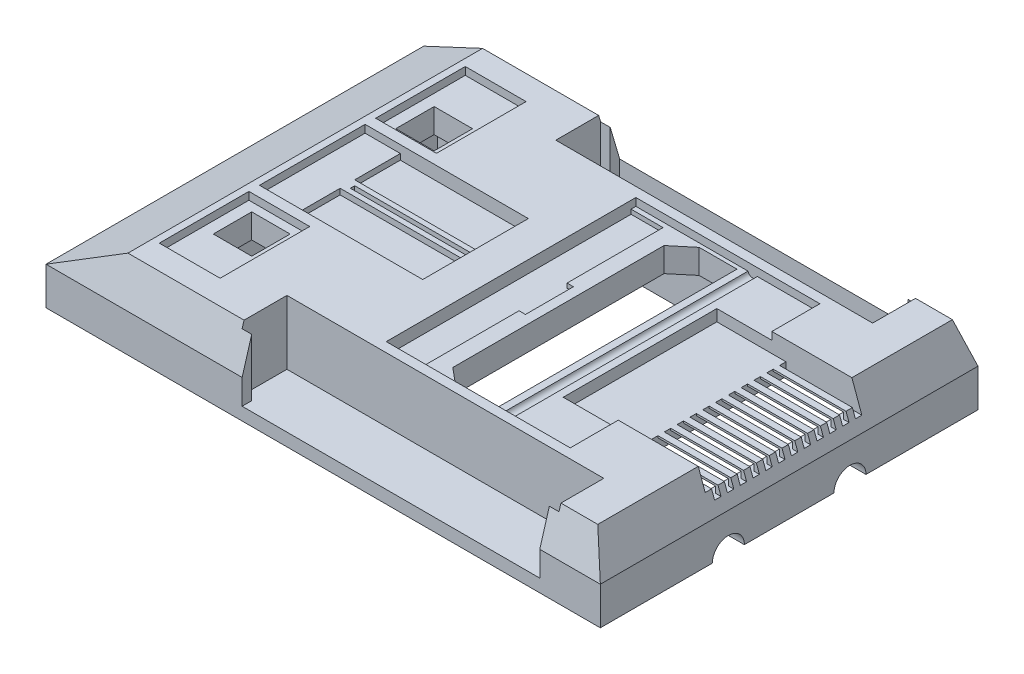
SolidWorks part; units mm, degrees
ref_plane "Front Plane" through (0, 0, 0) normal (0, 0, 1) x (1, 0, 0)
ref_plane "Top Plane" through (0, 0, 0) normal (0, 1, 0) x (1, 0, 0)
ref_plane "Right Plane" through (0, 0, 0) normal (1, 0, 0) x (0, 0, -1)
sketch "Sketch1" plane through (0, 0, 0) normal (0, 1, 0) x (1, 0, 0)
  line L1 (-219.964, -149.86) -> (0, -149.86)
  line L2 (-219.964, -149.86) -> (-219.964, 0)
  line L3 (-219.964, 0) -> (0, 0)
  line L4 (0, -149.86) -> (0, 0)
  dimension "D1" = 149.86
  dimension "D2" = 219.964
ref_plane "MiddleTop" through (0, 14.986, 0) normal (0, 1, 0) x (1, 0, 0)
sketch "Sketch2" plane through (0, 14.986, 0) normal (0, 1, 0) x (1, 0, 0)
  line L1 (0, 0) -> (-219.964, 0)
  line L2 (0, 0) -> (0, -149.86)
  line L3 (0, -149.86) -> (-219.964, -149.86)
  line L4 (-219.964, 0) -> (-219.964, -149.86)
extrude "Boss-Extrude1" add sketch "Sketch1" along normal blind 14.986
ref_plane "Plane2" through (0, 30.48, 0) normal (0, 1, 0) x (1, 0, 0)
sketch "Sketch3" plane through (0, 30.48, 0) normal (0, 1, 0) x (1, 0, 0)
  line L0 (0, -149.86) -> (-219.964, -149.86) construction
  line L1 (-192.024, -4.572) -> (-5.588, -4.572)
  line L2 (-192.024, -4.572) -> (-192.024, -145.288)
  line L3 (-192.024, -145.288) -> (-5.588, -145.288)
  line L4 (-5.588, -4.572) -> (-5.588, -145.288)
  line L5 (-219.964, 0) -> (-219.964, -149.86) construction
  line L6 (0, 0) -> (0, -149.86) construction
  dimension "D1" = 140.716
  dimension "D2" = 4.572
  dimension "D3" = 27.94
  dimension "D4" = 5.588
loft "Loft1" add profiles "Sketch2", "Sketch3"
sketch "Sketch4" plane through (0, 30.48, 0) normal (0, 1, 0) x (1, 0, 0)
  line L0 (-192.024, -145.288) -> (-5.588, -145.288) construction
  line L1 (-189.23, -135.636) -> (-165.1, -135.636)
  line L2 (-189.23, -135.636) -> (-189.23, -100.076)
  line L3 (-189.23, -100.076) -> (-165.1, -100.076)
  line L4 (-165.1, -135.636) -> (-165.1, -100.076)
  line L5 (-192.024, -4.572) -> (-192.024, -145.288) construction
  line L6 (-5.588, -4.572) -> (-192.024, -4.572) construction
  line L7 (-189.23, -49.784) -> (-165.1, -49.784)
  line L8 (-189.23, -49.784) -> (-189.23, -14.224)
  line L9 (-189.23, -14.224) -> (-165.1, -14.224)
  line L10 (-165.1, -49.784) -> (-165.1, -14.224)
  point P12 (-177.165, -14.224)
  dimension "D1" = 35.56
  dimension "D2" = 24.13
  dimension "D3" = 9.652
  dimension "D4" = 2.794
  dimension "D5" = 24.13
  dimension "D6" = 35.56
  dimension "D7" = 2.794
  dimension "D8" = 9.652
sketch "Sketch5" plane through (0, 30.48, 0) normal (0, 1, 0) x (1, 0, 0)
  line L0 (-189.23, -100.076) -> (-165.1, -100.076) construction
  line L1 (-189.23, -95.885) -> (-124.46, -95.885)
  line L2 (-189.23, -95.885) -> (-189.23, -53.975)
  line L3 (-189.23, -53.975) -> (-124.46, -53.975)
  line L4 (-124.46, -95.885) -> (-124.46, -53.975)
  line L5 (-192.024, -4.572) -> (-192.024, -145.288) construction
  dimension "D1" = 41.91
  dimension "D2" = 4.191
  dimension "D3" = 2.794
  dimension "D4" = 64.77
extrude "Cut-Extrude1" cut sketch "Sketch4" against normal blind 3.048
extrude "Cut-Extrude2" cut sketch "Sketch5" against normal blind 3.048
ref_plane "Plane3" through (0, 25.146, 0) normal (0, 1, 0) x (1, 0, 0)
sketch "Sketch6" plane through (0, 25.146, 0) normal (0, 1, 0) x (1, 0, 0)
  line L0 (-189.23, -53.975) -> (-189.23, -95.885) construction
  line L1 (-175.26, -72.0598) -> (-124.46, -72.0598)
  line L2 (-175.26, -72.0598) -> (-175.26, -77.851)
  line L3 (-175.26, -77.851) -> (-124.46, -77.851)
  line L4 (-124.46, -72.0598) -> (-124.46, -77.851)
  line L5 (-189.23, -95.885) -> (-124.46, -95.885) construction
  dimension "D1" = 50.8
  dimension "D2" = 13.97
  dimension "D3" = 5.7912
  dimension "D4" = 18.034
sketch "Sketch10" plane through (0, 30.48, 0) normal (0, 1, 0) x (1, 0, 0)
  line L6 (0, -16.7641) -> (0, 16.7641) construction
  line L10 (-145.9491, -146.0512) -> (-145.9491, -128.2712)
  line L13 (-145.9491, -128.2712) -> (-20.2191, -128.2712)
  line L16 (-20.2191, -128.2712) -> (-20.2191, -146.0512)
  line L21 (-20.2191, -146.0512) -> (-145.9491, -146.0512)
  line L24 (-16.7641, 0) -> (16.7641, 0) construction
  line L25 (-219.964, -74.93) -> (-5.588, -74.93) construction
  line L26 (-20.2191, -21.5888) -> (-20.2191, -3.8088)
  line L27 (-219.964, 0) -> (-219.964, -149.86) construction
  line L28 (-5.588, -145.288) -> (-5.588, -4.572) construction
  line L29 (-20.2191, -3.8088) -> (-145.9491, -3.8088)
  line L30 (-145.9491, -3.8088) -> (-145.9491, -21.5888)
  line L31 (-145.9491, -21.5888) -> (-20.2191, -21.5888)
  dimension "D1" = 17.78
  dimension "D2" = 20.2191
  dimension "D3" = 128.2712
  dimension "D5" = 125.73
extrude "Cut-Extrude5" cut sketch "Sketch10" against normal blind 25.4
sketch "Sketch15" plane through (0, 30.48, 0) normal (0, 1, 0) x (1, 0, 0)
  line L0 (-5.588, -145.288) -> (-5.588, -4.572) construction
  line L1 (-110.363, -25.4) -> (-37.338, -25.4)
  line L2 (-110.363, -25.4) -> (-110.363, -124.46)
  line L3 (-110.363, -124.46) -> (-37.338, -124.46)
  line L4 (-37.338, -25.4) -> (-37.338, -44.45)
  line L6 (-37.338, -44.45) -> (-59.182, -44.45)
  line L7 (-59.182, -44.45) -> (-59.182, -105.41)
  line L8 (-59.182, -105.41) -> (-37.338, -105.41)
  line L9 (-37.338, -105.41) -> (-37.338, -124.46)
  line L10 (0, 0) -> (-219.964, 0) construction
  dimension "D1" = 73.025
  dimension "D2" = 31.75
  dimension "D3" = 99.06
  dimension "D4" = 25.4
  dimension "D5" = 21.844
  dimension "D6" = 60.96
  dimension "D7" = 19.05
extrude "Cut-Extrude7" cut sketch "Sketch15" against normal blind 3.048
sketch "Sketch16" plane through (0, 30.48, 0) normal (0, 1, 0) x (1, 0, 0)
  line L1 (-59.182, -44.45) -> (0.508, -44.45)
  line L2 (-59.182, -44.45) -> (-59.182, -105.41)
  line L3 (-59.182, -105.41) -> (0.508, -105.41)
  line L4 (0.508, -44.45) -> (0.508, -105.41)
  dimension "D1" = 59.69
extrude "Cut-Extrude8" cut sketch "Sketch16" against normal blind 7.62
sketch "Sketch17" plane through (0, 30.48, 0) normal (0, 1, 0) x (1, 0, 0)
  line L1 (-110.363, -27.3038) -> (-97.663, -27.3038)
  line L2 (-110.363, -27.3038) -> (-110.363, -122.5538)
  line L3 (-110.363, -122.5538) -> (-97.663, -122.5538)
  line L4 (-97.663, -27.3038) -> (-97.663, -65.4038)
  line L5 (-97.663, -65.4038) -> (-95.123, -65.4038)
  line L6 (-95.123, -65.4038) -> (-95.123, -84.4538)
  line L7 (-95.123, -84.4538) -> (-97.663, -84.4538)
  line L8 (-97.663, -84.4538) -> (-97.663, -122.5538)
  line L9 (-37.338, -21.5888) -> (-110.363, -21.5888) construction
  line L11 (-124.46, -95.885) -> (-124.46, -53.975) construction
  dimension "D1" = 12.7
  dimension "D2" = 19.05
  dimension "D3" = 38.1
  dimension "D4" = 2.54
  dimension "D5" = 95.25
  dimension "D6" = 5.715
  dimension "D7" = 14.097
extrude "Cut-Extrude9" cut sketch "Sketch17" against normal blind 4.826
sketch "Sketch18" plane through (0, 30.48, 0) normal (0, 1, 0) x (1, 0, 0)
  line L0 (-83.71, -26.9228) -> (-91.313, -33.2728)
  line L1 (-83.71, -26.9228) -> (-68.724, -26.9228)
  line L2 (-91.313, -33.2728) -> (-91.313, -117.0928)
  line L3 (-83.71, -123.4428) -> (-68.724, -123.4428)
  line L4 (-68.724, -26.9228) -> (-68.724, -123.4428)
  line L5 (-83.71, -123.4428) -> (-91.313, -117.0928)
  line L8 (-95.123, -84.4538) -> (-95.123, -65.4038) construction
  line L9 (-145.9491, -21.5888) -> (-20.2191, -21.5888) construction
  dimension "D1" = 14.986
  dimension "D2" = 9.906
  dimension "D3" = 9.906
  dimension "D4" = 14.986
  dimension "D5" = 83.82
  dimension "D6" = 96.52
  dimension "D7" = 5.334
  dimension "D8" = 3.81
extrude "Cut-Extrude10" cut sketch "Sketch18" against normal through all
sketch "Sketch19" plane through (0, 30.48, 0) normal (0, 1, 0) x (1, 0, 0)
  line L0 (0, -149.86) -> (0, 0) construction
  line L1 (-31.75, -44.45) -> (0, -44.45)
  line L2 (-31.75, -44.45) -> (-31.75, -46.99)
  line L3 (-31.75, -46.99) -> (0, -46.99)
  line L4 (0, -44.45) -> (0, -46.99)
  line L5 (-2.8398, -44.45) -> (-59.182, -44.45) construction
  dimension "D1" = 2.54
  dimension "D2" = 31.75
  dimension "D3" = 0
extrude "Cut-Extrude11" cut sketch "Sketch19" against normal blind 10.922
pattern_linear "LPattern1" count 12 spacing 5.08 along (0, 0, 1) of "Cut-Extrude11"
ref_plane "Plane5" through (0, 0, 44.45) normal (0, 0, 1) x (1, 0, 0)
sketch "Sketch20" plane through (0, 0, 44.45) normal (0, 0, 1) x (1, 0, 0)
  line L1 (-31.75, 22.098) -> (-3.81, 22.098)
  line L2 (-31.75, 22.098) -> (-31.75, 19.558)
  line L3 (-31.75, 19.558) -> (-3.81, 19.558)
  line L4 (-3.81, 22.098) -> (-3.81, 19.558)
  line L5 (0, -16.7641) -> (0, 16.7641) construction
  line L7 (-5.588, 30.48) -> (-37.338, 30.48) construction
  dimension "D1" = 3.81
  dimension "D2" = 2.54
  dimension "D3" = 8.382
  dimension "D4" = 27.94
extrude "Cut-Extrude12" cut sketch "Sketch20" along normal blind 60.96
sketch "Sketch25" plane through (0, 30.48, 0) normal (0, 1, 0) x (1, 0, 0)
  line L1 (-175.26, -72.0598) -> (-124.46, -72.0598)
  line L2 (-175.26, -72.0598) -> (-175.26, -53.975)
  line L3 (-175.26, -53.975) -> (-124.46, -53.975)
  line L4 (-124.46, -72.0598) -> (-124.46, -53.975)
  line L5 (-175.26, -77.851) -> (-124.46, -77.851)
  line L6 (-175.26, -77.851) -> (-175.26, -95.885)
  line L7 (-175.26, -95.885) -> (-124.46, -95.885)
  line L8 (-124.46, -77.851) -> (-124.46, -95.885)
extrude "Cut-Extrude14" cut sketch "Sketch25" against normal blind 5.334
sketch "Sketch21" plane through (0, 30.48, 0) normal (0, 1, 0) x (1, 0, 0)
  line L1 (-173.228, -74.0918) -> (-126.238, -74.0918)
  line L2 (-173.228, -74.0918) -> (-173.228, -75.819)
  line L3 (-173.228, -75.819) -> (-126.238, -75.819)
  line L4 (-126.238, -74.0918) -> (-126.238, -75.819)
  line L7 (-124.46, -53.975) -> (-189.23, -53.975) construction
  line L8 (-175.26, -95.885) -> (-124.46, -95.885) construction
  line L9 (-124.46, -95.885) -> (-124.46, -53.975) construction
  dimension "D1" = 20.1168
  dimension "D2" = 20.066
  dimension "D3" = 46.99
  dimension "D4" = 1.778
extrude "Cut-Extrude13" cut sketch "Sketch21" against normal through all
ref_plane "Plane6" through (0, 0, 16.51) normal (0, 0, 1) x (1, 0, 0)
sketch "Sketch29" plane through (0, 0, 0) normal (0, 1, 0) x (1, 0, 0)
  line L1 (-190.4254, -24.13) -> (-7.5454, -24.13)
  line L2 (-190.4254, -24.13) -> (-190.4254, -125.73)
  line L3 (-190.4254, -125.73) -> (-7.5454, -125.73)
  line L4 (-7.5454, -24.13) -> (-7.5454, -125.73)
  line L6 (-16.7641, 0) -> (16.7641, 0) construction
  line L7 (0, -16.7641) -> (0, 16.7641) construction
  dimension "D1" = 101.6
  dimension "D2" = 182.88
  dimension "D3" = 24.13
  dimension "D4" = 7.5454
extrude "Cut-Extrude18" cut sketch "Sketch29" along normal blind 17.78
sketch "Sketch30" plane through (0, 30.48, 0) normal (0, 1, 0) x (1, 0, 0)
  line L0 (0, -16.7641) -> (0, 16.7641) construction
  line L1 (-184.6913, -46.355) -> (-169.4513, -46.355)
  line L2 (-184.6913, -46.355) -> (-184.6913, -31.115)
  line L3 (-184.6913, -31.115) -> (-169.4513, -31.115)
  line L4 (-169.4513, -46.355) -> (-169.4513, -31.115)
  line L7 (0, -74.93) -> (-237.3505, -74.93) construction
  line L8 (0, -149.86) -> (0, 0) construction
  line L9 (-184.6913, -118.745) -> (-169.4513, -118.745)
  line L10 (-169.4513, -103.505) -> (-169.4513, -118.745)
  line L11 (-184.6913, -103.505) -> (-169.4513, -103.505)
  line L12 (-184.6913, -103.505) -> (-184.6913, -118.745)
  line L13 (-16.7641, 0) -> (16.7641, 0) construction
  dimension "D1" = 15.24
  dimension "D2" = 15.24
  dimension "D3" = 169.4513
  dimension "D4" = 31.115
extrude "Cut-Extrude19" cut sketch "Sketch30" against normal through all
ref_plane "Plane7" through (0, 27.432, 0) normal (0, 1, 0) x (1, 0, 0)
sketch "Sketch32" plane through (0, 0, 0) normal (0, 1, 0) x (1, 0, 0)
  line L1 (-31.75, -44.45) -> (-6.35, -44.45)
  line L2 (-31.75, -44.45) -> (-31.75, -105.41)
  line L3 (-31.75, -105.41) -> (-6.35, -105.41)
  line L4 (-6.35, -44.45) -> (-6.35, -105.41)
  line L5 (-59.182, -105.41) -> (-2.8398, -105.41) construction
  point P7 (0, 0)
  dimension "D1" = 25.4
extrude "Cut-Extrude20" cut sketch "Sketch32" along normal blind 20.32
sketch "Sketch33" plane through (0, 0, 0) normal (1, 0, 0) x (0, 0, -1)
  line L0 (82.4231, 0) -> (-82.4231, 0) construction
  circle A0 centre (-99.06, 0) radius 6.35
  circle A1 centre (-50.8, 0) radius 6.35
  dimension "D3" = 12.7
  dimension "D4" = 12.7
  dimension "D1" = 50.8
  dimension "D2" = 50.8
extrude "Cut-Extrude21" cut sketch "Sketch33" against normal blind 19.05
ref_plane "Plane8" through (0, 0, 25.4) normal (0, 0, 1) x (1, 0, 0)
sketch "Sketch34" plane through (0, 0, 25.4) normal (0, 0, 1) x (1, 0, 0)
  line L0 (-20.2191, 27.8936) -> (-145.9491, 27.8936) construction
  circle A0 centre (-64.008, 27.8936) radius 1.905
  dimension "D2" = 3.81
  dimension "D1" = 58.42
extrude "Cut-Extrude22" cut sketch "Sketch34" along normal blind 99.06
sketch "Sketch35" plane through (0, 30.48, 0) normal (0, 1, 0) x (1, 0, 0)
  line L0 (-219.964, -149.86) -> (0, -149.86) construction
  line L1 (-142.1391, -149.86) -> (-24.0291, -149.86)
  line L2 (-142.1391, -149.86) -> (-142.1391, -143.51)
  line L3 (-142.1391, -143.51) -> (-24.0291, -143.51)
  line L4 (-24.0291, -149.86) -> (-24.0291, -143.51)
  line L5 (-145.9491, -128.2712) -> (-145.9491, -145.288) construction
  line L6 (-124.46, -74.9554) -> (15.5157, -74.9554) construction
  line L7 (-124.46, -72.0598) -> (-124.46, -77.851) construction
  line L8 (-24.0291, -0.0508) -> (-24.0291, -6.4008)
  line L9 (-142.1391, -0.0508) -> (-24.0291, -0.0508)
  line L10 (-142.1391, -0.0508) -> (-142.1391, -6.4008)
  line L11 (-142.1391, -6.4008) -> (-24.0291, -6.4008)
  point P6 (-142.1391, -146.685)
  dimension "D1" = 118.11
  dimension "D2" = 3.81
  dimension "D3" = 6.35
extrude "Cut-Extrude23" cut sketch "Sketch35" against normal blind 25.4
